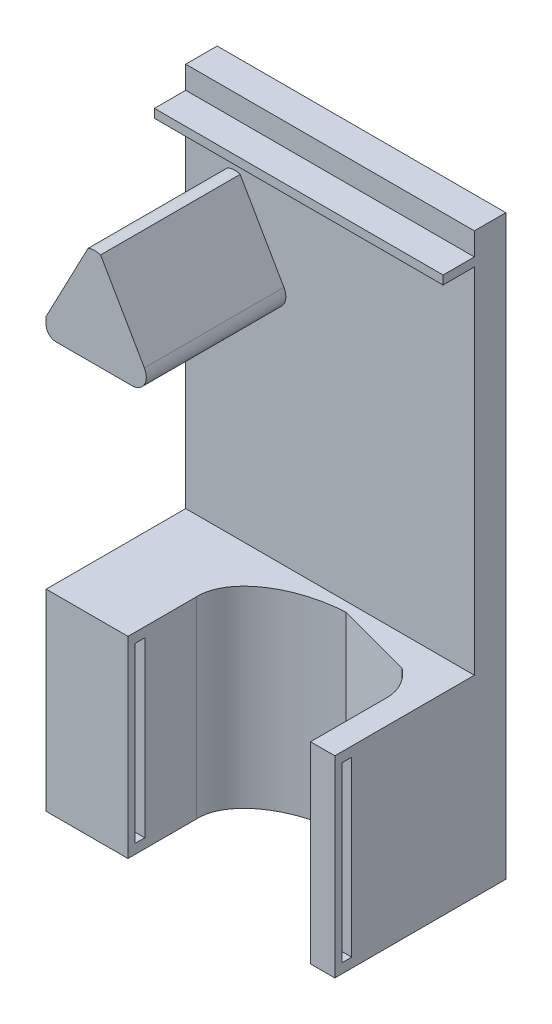
SolidWorks part; units mm, degrees
ref_plane "Front Plane" through (0, 0, 0) normal (0, 0, 1) x (1, 0, 0)
ref_plane "Top Plane" through (0, 0, 0) normal (0, 1, 0) x (1, 0, 0)
ref_plane "Right Plane" through (0, 0, 0) normal (1, 0, 0) x (0, 0, -1)
sketch "Sketch1" plane through (0, 0, 0) normal (0, 0, 1) x (1, 0, 0)
  line L1 (-30, 60) -> (30, 60)
  line L2 (-30, 60) -> (-30, -60)
  line L3 (-30, -60) -> (30, -60)
  line L4 (30, 60) -> (30, -60)
  line L5 (-30, 60) -> (30, -60) construction
  line L6 (-30, -60) -> (30, 60) construction
  point P0 (0, 0)
  dimension "D1" = 60
  dimension "D2" = 120
extrude "Boss-Extrude1" add sketch "Sketch1" along normal blind 6.54
sketch "Sketch7" plane through (0, 0, 6.54) normal (0, 0, 1) x (1, 0, 0)
  line L0 (-7, 25.5339) -> (-18.6841, 45.8173)
  line L1 (-30, 25.5339) -> (-7, 25.5339)
  line L6 (30, -60) -> (30, 60) construction
  line L15 (-21.295, 45.7034) -> (-30, 29.1154)
  line L16 (-30, 60) -> (-30, -60) construction
  line L18 (-30, 29.1154) -> (-30, 25.5339)
  line L19 (30, 60) -> (-30, 60) construction
  arc A1 (-21.295, 45.7034) -> (-18.6841, 45.8173) centre (-19.8396, 42.325) cw
  point P3 (-20, 46)
  point P9 (0, 0)
  point P10 (-18.546, 45.0415)
  point P13 (-22.3654, 44.7194)
  point P16 (-18.6841, 45.7034)
  dimension "D1" = 14
  dimension "D3" = 23
  dimension "D4" = 37
  dimension "D2" = 50
sketch "Sketch10" plane through (0, 0, 0) normal (0, 0, -1) x (-1, 0, 0)
  line L1 (20, 20) -> (26.54, 20)
  line L2 (-20, -25) -> (-20, 20)
  line L4 (-20, 20) -> (-26.54, 20)
  line L7 (20, -25) -> (20, 20)
  line L10 (-26.54, 20) -> (-26.54, -25)
  line L11 (-26.54, -25) -> (-20, -25)
  line L12 (26.54, 20) -> (26.54, -25)
  line L13 (26.54, -25) -> (20, -25)
  dimension "D1" = 6.54
  dimension "D2" = 20
  dimension "D3" = 6.54
  dimension "D4" = 20
  dimension "D5" = 45
  dimension "D6" = 45
sketch "Sketch17" plane through (0, 0, 6.54) normal (0, 0, 1) x (1, 0, 0)
  line L0 (-30, 60) -> (-30, -60) construction
  line L1 (-30, -20) -> (30, -20)
  line L2 (-30, -20) -> (-30, -60)
  line L3 (-30, -60) -> (30, -60)
  line L4 (30, -20) -> (30, -60)
  line L5 (30, -60) -> (30, 60) construction
  line L6 (-30, -60) -> (30, -60) construction
  line L7 (30, 60) -> (-30, 60) construction
  dimension "D1" = 40
  dimension "D2" = 0
  dimension "D3" = 80
extrude "Boss-Extrude6" add sketch "Sketch17" along normal blind 29
sketch "Sketch18" plane through (0, -20, 0) normal (0, 1, 0) x (1, 0, 0)
  line L0 (5.335, -8.5264) -> (21.2913, -12.8258)
  line L1 (30, -35.54) -> (30, -6.54) construction
  line L2 (30, -35.54) -> (-30, -35.54) construction
  ellipse E0 centre (5.9723, -20.3092) end of major axis (24.9445, -19.283) minor radius 11.8 (5.335, -8.5264) -> (21.2913, -12.8258) ccw
  dimension "D1" = 43
  dimension "D2" = 5.0555
  dimension "D3" = 3.448
extrude "Cut-Extrude1" cut sketch "Sketch18" against normal up to next contours E0 L0
sketch "Sketch21" plane through (0, 0, 35.54) normal (0, 0, 1) x (1, 0, 0)
  line L0 (30, -20) -> (-30, -20) construction
  line L1 (-13, -20) -> (24.9445, -20)
  line L2 (-13, -20) -> (-13, -60)
  line L3 (-13, -60) -> (24.9445, -60)
  line L4 (24.9445, -20) -> (24.9445, -60)
  line L5 (-30, -60) -> (30, -60) construction
  line L6 (30, -60) -> (30, -20) construction
  dimension "D1" = 5.0555
  dimension "D2" = 43
extrude "Cut-Extrude2" cut sketch "Sketch21" against normal up to next contours L2 L3 L4 L1
sketch "Sketch23" plane through (-13, 0, 0) normal (1, 0, 0) x (0, 0, -1)
  line L0 (-35.54, -20) -> (-35.54, -60) construction
  line L1 (-34.04, -22) -> (-32.04, -22)
  line L2 (-34.04, -22) -> (-34.04, -58)
  line L3 (-34.04, -58) -> (-32.04, -58)
  line L4 (-32.04, -22) -> (-32.04, -58)
  line L5 (-21.3353, -60) -> (-35.54, -60) construction
  line L6 (-21.3353, -20) -> (-35.54, -20) construction
  dimension "D1" = 3.5
  dimension "D2" = 2
  dimension "D3" = 2
  dimension "D4" = 2
  dimension "D5" = 36
extrude "Cut-Extrude3" cut sketch "Sketch23" against normal blind 9
sketch "Sketch24" plane through (24.9445, 0, 0) normal (-1, 0, 0) x (0, 0, 1)
  line L0 (20.076, -60) -> (35.54, -60) construction
  line L1 (32.04, -22) -> (34.04, -22)
  line L2 (32.04, -22) -> (32.04, -58)
  line L3 (32.04, -58) -> (34.04, -58)
  line L4 (34.04, -22) -> (34.04, -58)
  line L5 (20.076, -20) -> (35.54, -20) construction
  line L6 (35.54, -20) -> (35.54, -60) construction
  dimension "D1" = 2
  dimension "D2" = 2
  dimension "D3" = 2
  dimension "D4" = 3.5
extrude "Cut-Extrude4" cut sketch "Sketch24" against normal blind 9
extrude "Boss-Extrude8" add sketch "Sketch7" along normal blind 29
sketch "Sketch36" plane through (0, 0, 6.54) normal (0, 0, 1) x (1, 0, 0)
  line L0 (-30, 53.5) -> (30, 53.5)
  line L1 (30, 60) -> (-30, 60) construction
  line L2 (-30, 60) -> (-30, 29.1154) construction
  line L3 (-30, 55.3) -> (30, 55.3)
  line L4 (30, -20) -> (30, 60) construction
  line L5 (-30, 55.3) -> (-30, 53.5)
  line L6 (30, 55.3) -> (30, 53.5)
  dimension "D1" = 6.5
  dimension "D2" = 4.7
extrude "Boss-Extrude9" add sketch "Sketch36" along normal blind 6.5
fillet "Fillet1" radius 3 1 edges at (-7, 25.5339, 21.04)
fillet "Fillet2" radius 2 1 edges at (-30, 25.5339, 21.04)
sketch "Sketch38" plane through (0, 0, 6.54) normal (0, 0, 1) x (1, 0, 0)
  line L0 (-9.1903, 28.5339) -> (-9.1903, -36.6848) construction
  line L1 (30, -20) -> (30, 53.5) construction
  arc A0 (-12.1903, 25.5339) -> (-9.5907, 30.0314) centre (-12.1903, 28.5339) ccw construction
  arc A1 (-12.1903, 25.5339) -> (-9.5907, 30.0314) centre (-12.1903, 28.5339) ccw construction
  dimension "D1" = 39.1903
